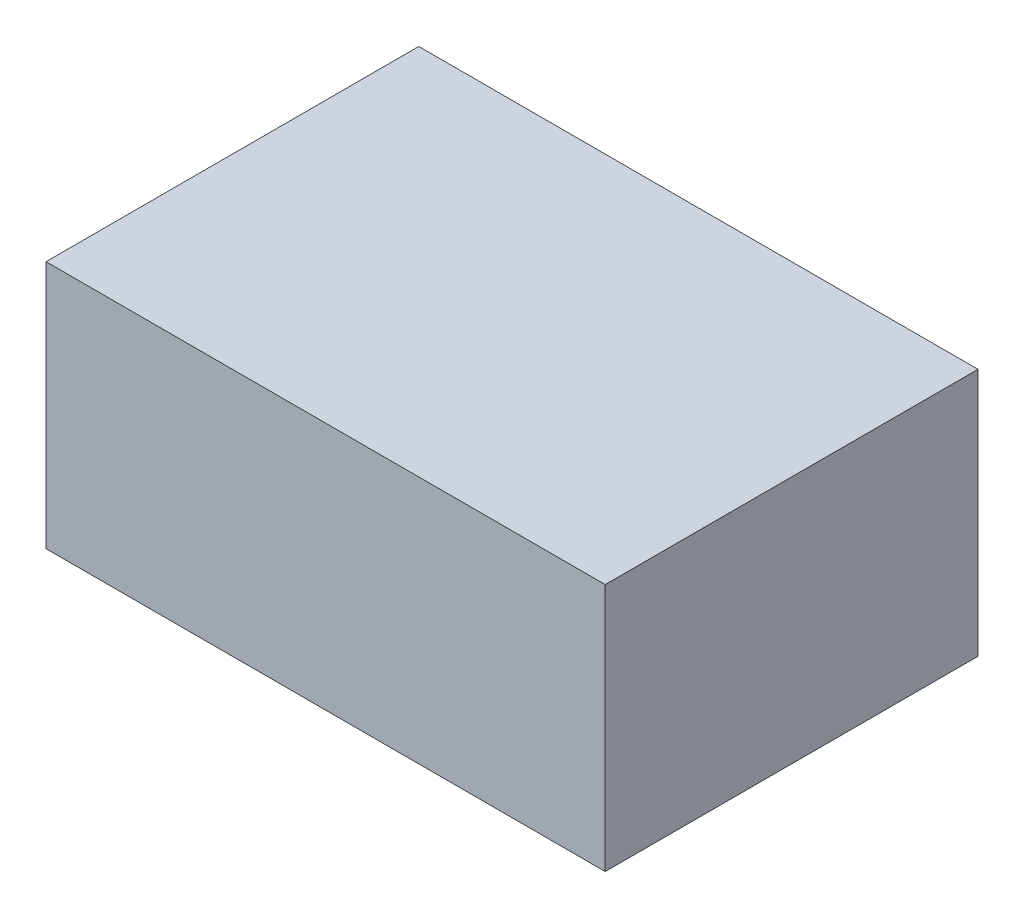
SolidWorks part; units mm, degrees
ref_plane "前视基准面" through (0, 0, 0) normal (0, 0, 1) x (1, 0, 0)
ref_plane "上视基准面" through (0, 0, 0) normal (0, 1, 0) x (1, 0, 0)
ref_plane "右视基准面" through (0, 0, 0) normal (1, 0, 0) x (0, 0, -1)
other "Configuration Table"
sketch "Sketch1" plane through (0, 0, 0) normal (0, 1, 0) x (1, 0, 0)
  line L1 (45, -30) -> (-45, -30)
  line L2 (45, -30) -> (45, 30)
  line L3 (45, 30) -> (-45, 30)
  line L4 (-45, -30) -> (-45, 30)
  line L5 (45, -30) -> (-45, 30) construction
  line L6 (45, 30) -> (-45, -30) construction
  point P0 (0, 0)
  dimension "D1" = 60
  dimension "D2" = 90
extrude "Boss-Extrude2" add sketch "Sketch1" along normal blind 40
sketch "Sketch3" plane through (0, 0, 0) normal (0, -1, 0) x (-1, 0, 0)
  line L0 (0, -21.5) -> (0, 21.5) construction
  line L1 (40, 21.5) -> (-40, 21.5) construction
  line L2 (40, 21.5) -> (40, -21.5) construction
  line L3 (40, -21.5) -> (-40, -21.5) construction
  line L4 (-40, 21.5) -> (-40, -21.5) construction
  line L5 (40, 21.5) -> (-40, -21.5) construction
  line L6 (40, -21.5) -> (-40, 21.5) construction
  line L7 (40, 0) -> (-40, 0) construction
  circle A0 centre (40, -21.5) radius 1.6
  circle A1 centre (-40, -21.5) radius 1.6
  circle A2 centre (-40, 21.5) radius 1.6
  circle A3 centre (40, 21.5) radius 1.6
  point P0 (0, 0)
  dimension "D3" = 3.2
  dimension "D1" = 43
  dimension "D2" = 80
extrude "Cut-Extrude1" cut sketch "Sketch3" against normal blind 10
